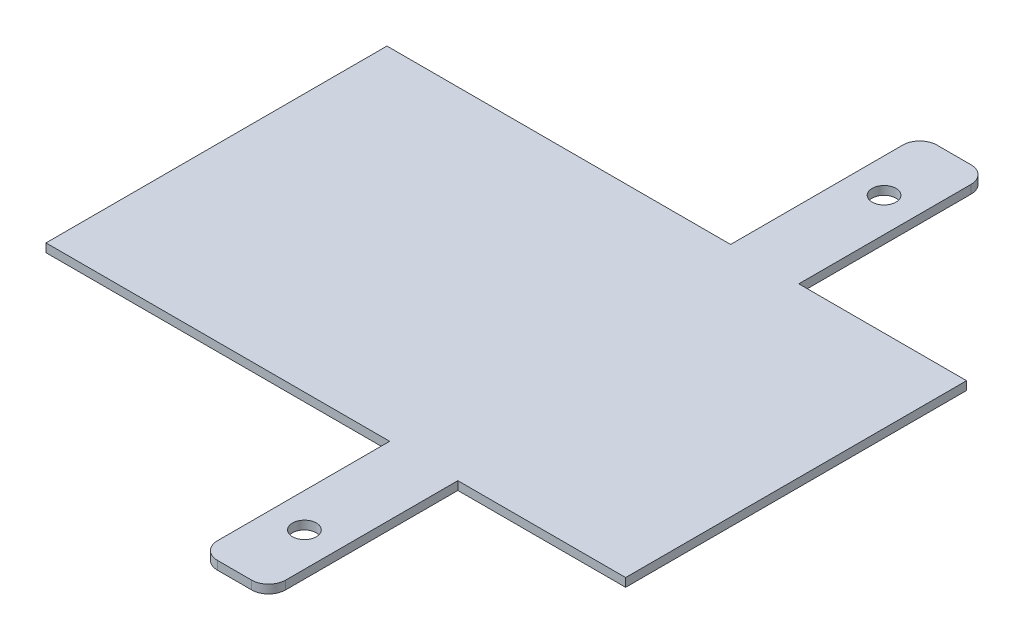
SolidWorks part; units mm, degrees
ref_plane "Front" through (0, 0, 0) normal (0, 0, 1) x (1, 0, 0)
ref_plane "Top" through (0, 0, 0) normal (0, 1, 0) x (1, 0, 0)
ref_plane "Right" through (0, 0, 0) normal (1, 0, 0) x (0, 0, -1)
sketch "Sketch1" plane through (0, 0, 0) normal (0, 1, 0) x (1, 0, 0)
  line L0 (-449.7086, 422.6316) -> (-351.2965, 422.6316)
  line L1 (-691.2965, 422.6316) -> (-489.7086, 422.6316)
  line L2 (-691.2965, 422.6316) -> (-691.2965, 222.6316)
  line L3 (-691.2965, 222.6316) -> (-489.7086, 222.6316)
  line L4 (-351.2965, 422.6316) -> (-351.2965, 222.6316)
  line L6 (-489.7086, 422.6316) -> (-489.7086, 523.6316)
  line L7 (-479.7086, 533.6316) -> (-459.7086, 533.6316)
  line L8 (-449.7086, 422.6316) -> (-449.7086, 523.6316)
  line L9 (-351.2965, 322.6316) -> (-691.2965, 322.6316) construction
  line L10 (-449.7086, 222.6316) -> (-449.7086, 121.6316)
  line L11 (-479.7086, 111.6316) -> (-459.7086, 111.6316)
  line L12 (-489.7086, 222.6316) -> (-489.7086, 121.6316)
  line L13 (-449.7086, 222.6316) -> (-351.2965, 222.6316)
  arc A0 (-459.7086, 533.6316) -> (-449.7086, 523.6316) centre (-459.7086, 523.6316) cw
  arc A1 (-489.7086, 523.6316) -> (-479.7086, 533.6316) centre (-479.7086, 523.6316) cw
  arc A2 (-489.7086, 121.6316) -> (-479.7086, 111.6316) centre (-479.7086, 121.6316) ccw
  arc A3 (-459.7086, 111.6316) -> (-449.7086, 121.6316) centre (-459.7086, 121.6316) ccw
  circle A4 centre (-469.7086, 492.6316) radius 7
  circle A5 centre (-469.7086, 152.6316) radius 7
  point P10 (-449.7086, 533.6316)
  point P13 (-489.7086, 533.6316)
  point P24 (-489.7086, 111.6316)
  point P25 (-449.7086, 111.6316)
  dimension "D5" = 10
  dimension "D6" = 340
  dimension "D8" = 118.4122
  dimension "D1" = 340
  dimension "D2" = 200
  dimension "D3" = 40
  dimension "D4" = 111
  dimension "D7" = 170
  dimension "D9" = 20
extrude "Boss-Extrude1" add sketch "Sketch1" along normal blind 5
